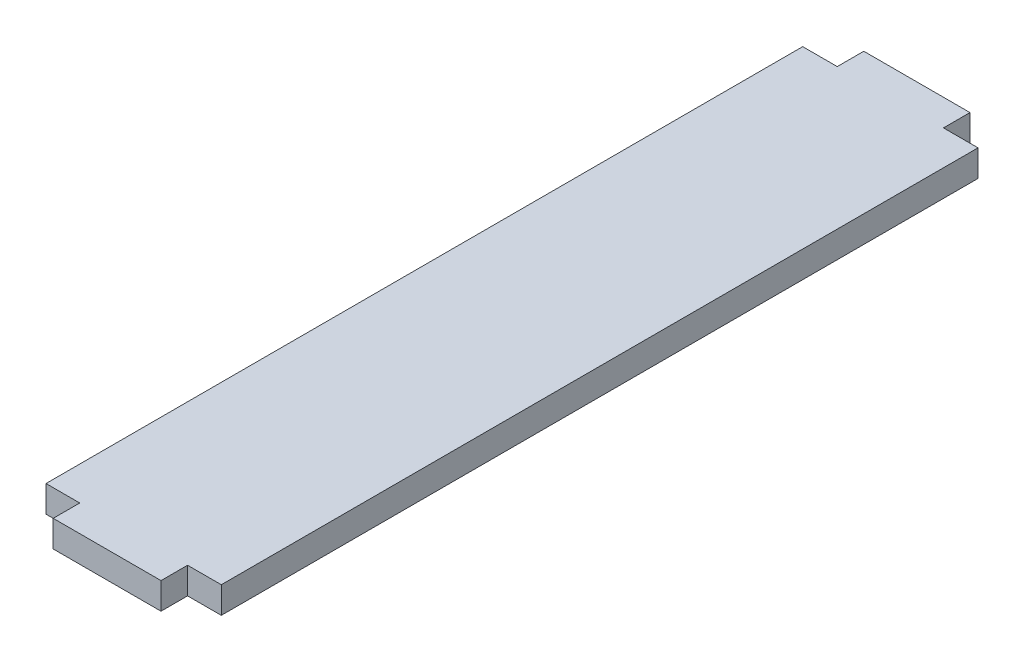
SolidWorks part; units mm, degrees
ref_plane "Front Plane" through (0, 0, 0) normal (0, 0, 1) x (1, 0, 0)
ref_plane "Top Plane" through (0, 0, 0) normal (0, 1, 0) x (1, 0, 0)
ref_plane "Right Plane" through (0, 0, 0) normal (1, 0, 0) x (0, 0, -1)
sketch "Sketch1" plane through (0, 0, 0) normal (0, 1, 0) x (1, 0, 0)
  line L1 (0, 0) -> (-33.54, 0)
  line L2 (0, 0) -> (0, 144.78)
  line L3 (0, 144.78) -> (-33.54, 144.78)
  line L4 (-33.54, 0) -> (-33.54, 144.78)
  dimension "D1" = 144.78
  dimension "D2" = 33.54
extrude "Boss-Extrude1" add sketch "Sketch1" along normal blind 5.08
sketch "Sketch2" plane through (0, 0, -144.78) normal (0, 0, -1) x (-1, 0, 0)
  line L0 (0, 0) -> (6.61, 0) construction
  line L1 (0, 0) -> (33.54, 0) construction
  line L2 (6.61, 0) -> (26.93, 0) construction
  line L3 (26.93, 0) -> (33.54, 0) construction
  line L4 (33.54, 5.08) -> (33.54, 0) construction
  line L5 (0, 5.08) -> (33.54, 5.08) construction
  line L6 (26.93, 0) -> (6.61, 0)
  line L7 (26.93, 0) -> (26.93, 5.08)
  line L8 (26.93, 5.08) -> (6.61, 5.08)
  line L9 (6.61, 0) -> (6.61, 5.08)
  dimension "D1" = 20.32
extrude "Boss-Extrude2" add sketch "Sketch2" along normal blind 5.08
sketch "Sketch3" plane through (0, 0, 0) normal (0, 0, 1) x (1, 0, 0)
  line L0 (0, 0) -> (-6.455, 0) construction
  line L1 (-33.54, 0) -> (0, 0) construction
  line L2 (-6.455, 0) -> (-27.085, 0) construction
  line L3 (-27.085, 0) -> (-33.54, 0) construction
  line L4 (-33.54, 5.08) -> (0, 5.08) construction
  line L5 (-27.085, 0) -> (-6.455, 0)
  line L6 (-27.085, 0) -> (-27.085, 5.08)
  line L7 (-27.085, 5.08) -> (-6.455, 5.08)
  line L8 (-6.455, 0) -> (-6.455, 5.08)
  dimension "D1" = 20.63
extrude "Boss-Extrude3" add sketch "Sketch3" along normal blind 5.08
equation "\"MDFThickness\"= .2in"
equation "\"D1@Boss-Extrude1\"=\"MDFThickness\""
equation "\"D1@Boss-Extrude2\"=\"MDFThickness\""
equation "\"D1@Boss-Extrude3\"=\"MDFThickness\""
